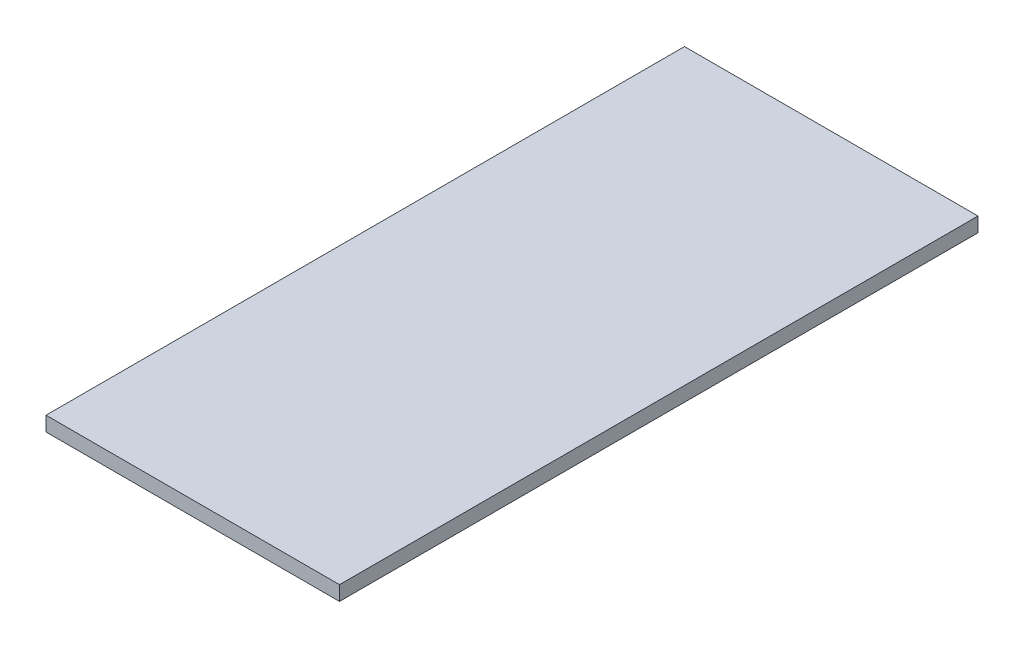
SolidWorks part; units mm, degrees
ref_plane "Front Plane" through (0, 0, 0) normal (0, 0, 1) x (1, 0, 0)
ref_plane "Top Plane" through (0, 0, 0) normal (0, 1, 0) x (1, 0, 0)
ref_plane "Right Plane" through (0, 0, 0) normal (1, 0, 0) x (0, 0, -1)
sketch "Sketch1" plane through (0, 39.6047, 0) normal (0, -1, 0) x (1, 0, 0)
  line L1 (-102.6996, 531.9985) -> (119.2344, 531.9985)
  line L3 (-102.6996, 49.1767) -> (119.2344, 49.1767)
  line L4 (-102.6996, 49.1767) -> (-102.6996, 531.9985)
  line L6 (119.2344, 49.1767) -> (119.2344, 531.9985)
extrude "Boss-Extrude1" add sketch "Sketch1" along normal blind 11
